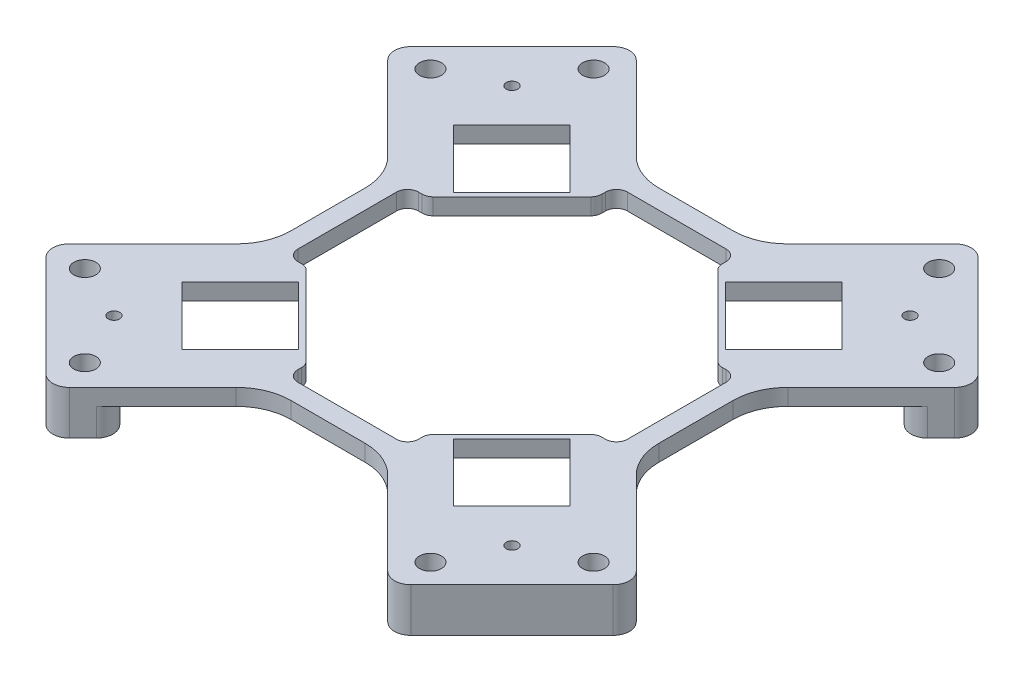
SolidWorks part; units mm, degrees
ref_plane "Front Plane" through (0, 0, 0) normal (0, 0, 1) x (1, 0, 0)
ref_plane "Top Plane" through (0, 0, 0) normal (0, 1, 0) x (1, 0, 0)
ref_plane "Right Plane" through (0, 0, 0) normal (1, 0, 0) x (0, 0, -1)
sketch "Sketch1" plane through (0, 0, 0) normal (0, 1, 0) x (1, 0, 0)
  line L0 (0, 0) -> (38.8909, 38.8909) construction
  line L1 (0, 0) -> (0, 62.2782) construction
  line L2 (0, 0) -> (67.5007, 0) construction
  line L3 (31.4663, 46.3155) -> (46.3155, 31.4663) construction
  circle A0 centre (31.4663, 46.3155) radius 2
  circle A1 centre (46.3155, 31.4663) radius 2
  circle A2 centre (46.3155, -31.4663) radius 2
  circle A3 centre (31.4663, -46.3155) radius 2
  circle A4 centre (-31.4663, -46.3155) radius 2
  circle A5 centre (-46.3155, -31.4663) radius 2
  circle A6 centre (-46.3155, 31.4663) radius 2
  circle A7 centre (-31.4663, 46.3155) radius 2
  dimension "D2" = 4
  dimension "D3" = 21
  dimension "D4" = 110
  dimension "D1" = 45
sketch "Sketch2" plane through (0, 0, 0) normal (0, 1, 0) x (1, 0, 0)
  line L0 (0, 0) -> (-24.7487, 24.7487) construction
  line L1 (0, 0) -> (0, 43.8991) construction
  line L2 (-30.052, 19.4454) -> (-19.4454, 30.052) construction
  line L3 (-35.3553, 24.7487) -> (-24.7487, 35.3553)
  line L4 (-24.7487, 35.3553) -> (-14.1421, 24.7487)
  line L5 (-14.1421, 24.7487) -> (-24.7487, 14.1421)
  line L6 (-24.7487, 14.1421) -> (-35.3553, 24.7487)
  line L7 (14.1421, 24.7487) -> (24.7487, 14.1421)
  line L8 (24.7487, 14.1421) -> (35.3553, 24.7487)
  line L9 (35.3553, 24.7487) -> (24.7487, 35.3553)
  line L10 (24.7487, 35.3553) -> (14.1421, 24.7487)
  line L11 (0, 0) -> (-30.052, 0) construction
  line L12 (-14.1421, -24.7487) -> (-24.7487, -14.1421)
  line L13 (-24.7487, -14.1421) -> (-35.3553, -24.7487)
  line L14 (-35.3553, -24.7487) -> (-24.7487, -35.3553)
  line L15 (-24.7487, -35.3553) -> (-14.1421, -24.7487)
  line L16 (14.1421, -24.7487) -> (24.7487, -14.1421)
  line L17 (24.7487, -35.3553) -> (14.1421, -24.7487)
  line L18 (35.3553, -24.7487) -> (24.7487, -35.3553)
  line L19 (24.7487, -14.1421) -> (35.3553, -24.7487)
  dimension "D1" = 45
  dimension "D2" = 15
  dimension "D3" = 15
  dimension "D4" = 35
sketch "Sketch3" plane through (0, 0, 0) normal (0, 1, 0) x (1, 0, 0)
  line L0 (-53.7401, 31.1127) -> (-31.1127, 53.7401)
  line L1 (-31.1127, 53.7401) -> (31.1127, 53.7401)
  line L2 (31.1127, 53.7401) -> (53.7401, 31.1127)
  line L3 (53.7401, 31.1127) -> (53.7401, -31.1127)
  line L4 (53.7401, -31.1127) -> (31.1127, -53.7401)
  line L5 (31.1127, -53.7401) -> (-31.1127, -53.7401)
  line L6 (-31.1127, -53.7401) -> (-53.7401, -31.1127)
  line L7 (-53.7401, -31.1127) -> (-53.7401, 31.1127)
  line L8 (0, 0) -> (60.9174, 0) construction
  line L9 (0, 0) -> (0, 56.6355) construction
  dimension "D1" = 32
  dimension "D3" = 120
extrude "Boss-Extrude1" add sketch "Sketch3" along normal blind 3
sketch "Sketch4" plane through (0, 0, 0) normal (0, -1, 0) x (-1, 0, 0)
  line L0 (53.7401, -31.1127) -> (31.1127, -53.7401)
  line L1 (31.1127, -53.7401) -> (24.3952, -47.0226)
  line L3 (24.3952, -47.0226) -> (47.0226, -24.3952)
  line L5 (47.0226, -24.3952) -> (53.7401, -31.1127)
  line L6 (0, 0) -> (0, 69.2529) construction
  line L7 (0, 0) -> (88.6109, 0) construction
  line L8 (31.1127, 53.7401) -> (24.3952, 47.0226)
  line L9 (53.7401, 31.1127) -> (31.1127, 53.7401)
  line L10 (47.0226, 24.3952) -> (53.7401, 31.1127)
  line L11 (24.3952, 47.0226) -> (47.0226, 24.3952)
  line L12 (-31.1127, 53.7401) -> (-24.3952, 47.0226)
  line L13 (-53.7401, 31.1127) -> (-31.1127, 53.7401)
  line L14 (-47.0226, 24.3952) -> (-53.7401, 31.1127)
  line L15 (-24.3952, 47.0226) -> (-47.0226, 24.3952)
  line L16 (-47.0226, -24.3952) -> (-53.7401, -31.1127)
  line L17 (-53.7401, -31.1127) -> (-31.1127, -53.7401)
  line L18 (-31.1127, -53.7401) -> (-24.3952, -47.0226)
  line L19 (-24.3952, -47.0226) -> (-47.0226, -24.3952)
  dimension "D1" = 9.5
extrude "Boss-Extrude2" add sketch "Sketch4" along normal blind 5
extrude "Cut-Extrude1" cut sketch "Sketch2" along normal blind 3
extrude "Cut-Extrude2" cut sketch "Sketch1" along normal through all and the other way through all
sketch "Sketch5" plane through (0, 0, 0) normal (0, 1, 0) x (1, 0, 0)
  line L0 (-53.7401, -31.1127) -> (-33.5, -10.8726)
  line L1 (-33.5, -10.8726) -> (-33.5, 10.8726)
  line L2 (-33.5, 10.8726) -> (-53.7401, 31.1127)
  line L3 (-47.0226, 24.3952) -> (-53.7401, 31.1127) construction
  line L4 (-53.7401, 31.1127) -> (-53.7401, -31.1127) construction
  line L5 (-53.7401, 31.1127) -> (-53.7401, -31.1127)
  line L6 (53.7401, -31.1127) -> (33.5, -10.8726)
  line L7 (33.5, -10.8726) -> (33.5, 10.8726)
  line L8 (33.5, 10.8726) -> (53.7401, 31.1127)
  line L9 (53.7401, 31.1127) -> (53.7401, -31.1127)
  line L10 (0, 0) -> (0, 62.7351) construction
  line L11 (-53.7401, 0) -> (53.7401, 0) construction
  line L13 (-31.1127, -53.7401) -> (31.1127, -53.7401)
  line L14 (-31.1127, -53.7401) -> (31.1127, -53.7401) construction
  line L15 (31.1127, -53.7401) -> (10.8726, -33.5)
  line L16 (10.8726, -33.5) -> (-10.8726, -33.5)
  line L17 (-10.8726, -33.5) -> (-31.1127, -53.7401)
  line L18 (-31.1127, 53.7401) -> (31.1127, 53.7401)
  line L19 (31.1127, 53.7401) -> (10.8726, 33.5)
  line L20 (10.8726, 33.5) -> (-10.8726, 33.5)
  line L21 (-10.8726, 33.5) -> (-31.1127, 53.7401)
  dimension "D1" = 67
  dimension "D2" = 45
  dimension "D3" = 67
  dimension "D4" = 45
extrude "Cut-Extrude4" cut sketch "Sketch5" along normal blind 10
fillet "Fillet1" radius 3 16 edges at (-47.0226, -2.5, 24.3952) (-53.7401, -1, 31.1127) (-31.1127, -1, 53.7401) (-24.3952, -2.5, 47.0226) (24.3952, -2.5, 47.0226) (31.1127, -1, 53.7401) (47.0226, -2.5, 24.3952) (53.7401, -1, 31.1127) (47.0226, -2.5, -24.3952) (53.7401, -1, -31.1127) (31.1127, -1, -53.7401) (24.3952, -2.5, -47.0226) (-47.0226, -2.5, -24.3952) (-53.7401, -1, -31.1127) (-24.3952, -2.5, -47.0226) (-31.1127, -1, -53.7401)
fillet "Fillet2" radius 10 8 edges at (33.5, 1.5, 10.8726) (33.5, 1.5, -10.8726) (10.8726, 1.5, -33.5) (-10.8726, 1.5, -33.5) (-33.5, 1.5, -10.8726) (-33.5, 1.5, 10.8726) (-10.8726, 1.5, 33.5) (10.8726, 1.5, 33.5)
sketch "Sketch8" plane through (0, 0, 0) normal (0, -1, 0) x (1, 0, 0)
  line L0 (0, 0) -> (-17.0913, 17.0913) construction
  line L1 (0, 0) -> (17.0913, 17.0913) construction
  line L2 (0, 0) -> (0, 30.4732) construction
  line L3 (-26.5, 10.9767) -> (-10.9767, 26.5)
  line L4 (-10.9767, 26.5) -> (10.9767, 26.5)
  line L5 (10.9767, 26.5) -> (26.5, 10.9767)
  line L6 (26.5, 10.9767) -> (26.5, -10.9767)
  line L7 (26.5, -10.9767) -> (10.9767, -26.5)
  line L8 (10.9767, -26.5) -> (-10.9767, -26.5)
  line L9 (-10.9767, -26.5) -> (-26.5, -10.9767)
  line L10 (-26.5, -10.9767) -> (-26.5, 10.9767)
  line L11 (0, 26.5) -> (0, -26.5) construction
  line L12 (-26.5, 0) -> (26.5, 0) construction
  line L13 (24.7487, 14.1421) -> (14.1421, 24.7487) construction
  dimension "D1" = 45
  dimension "D2" = 1
extrude "Cut-Extrude5" cut sketch "Sketch8" against normal blind 10
sketch "Sketch9" plane through (0, 0, 0) normal (0, -1, 0) x (1, 0, 0)
  line L0 (0, 0) -> (0, 53.3985) construction
  line L1 (-30, -10.9767) -> (-25, -10.9767)
  line L2 (-30, -10.9767) -> (-30, 10.9767)
  line L3 (-30, 10.9767) -> (-25, 10.9767)
  line L4 (-25, -10.9767) -> (-25, 10.9767)
  line L5 (-10.9767, 25) -> (10.9767, 25)
  line L6 (-10.9767, 25) -> (-10.9767, 30)
  line L7 (-10.9767, 30) -> (10.9767, 30)
  line L8 (10.9767, 25) -> (10.9767, 30)
  line L9 (30, -10.9767) -> (25, -10.9767)
  line L10 (30, -10.9767) -> (30, 10.9767)
  line L11 (30, 10.9767) -> (25, 10.9767)
  line L12 (25, -10.9767) -> (25, 10.9767)
  line L13 (-10.9767, -25) -> (10.9767, -25)
  line L14 (-10.9767, -25) -> (-10.9767, -30)
  line L15 (-10.9767, -30) -> (10.9767, -30)
  line L16 (10.9767, -25) -> (10.9767, -30)
  line L17 (0, 0) -> (-45.8524, 0) construction
  dimension "D1" = 50
  dimension "D2" = 50
  dimension "D3" = 60
  dimension "D4" = 60
extrude "Cut-Extrude6" cut sketch "Sketch9" against normal blind 10
fillet "Fillet3" radius 2 16 edges at (-10.9767, 1.5, 26.5) (-10.9767, 1.5, 30) (10.9767, 1.5, 30) (10.9767, 1.5, 26.5) (26.5, 1.5, 10.9767) (30, 1.5, 10.9767) (30, 1.5, -10.9767) (26.5, 1.5, -10.9767) (10.9767, 1.5, -26.5) (10.9767, 1.5, -30) (-10.9767, 1.5, -30) (-10.9767, 1.5, -26.5) (-26.5, 1.5, -10.9767) (-26.5, 1.5, 10.9767) (-30, 1.5, 10.9767) (-30, 1.5, -10.9767)
sketch "Sketch10" plane through (0, 0, 0) normal (0, 1, 0) x (1, 0, 0)
  line L0 (36.2392, 36.2392) -> (-36.2392, -36.2392) construction
  line L1 (-36.2392, 36.2392) -> (36.2392, -36.2392) construction
  line L2 (0, 0) -> (-21.423, 0) construction
  circle A0 centre (36.2392, 36.2392) radius 1.05
  circle A1 centre (-36.2392, -36.2392) radius 1.05
  circle A2 centre (-36.2392, 36.2392) radius 1.05
  circle A3 centre (36.2392, -36.2392) radius 1.05
  dimension "D1" = 2.1
  dimension "D2" = 102.5
  dimension "D3" = 102.5
  dimension "D4" = 45
extrude "Cut-Extrude7" cut sketch "Sketch10" against normal blind 10 and the other way blind 10
sketch "Sketch11" plane through (0, 0, 0) normal (0, -1, 0) x (1, 0, 0)
  circle A0 centre (36.2392, -36.2392) radius 4
  circle A1 centre (-36.2392, 36.2392) radius 4
  circle A2 centre (-36.2392, -36.2392) radius 4
  circle A3 centre (36.2392, 36.2392) radius 4
  circle A4 centre (-36.2392, 36.2392) radius 1.05
  arc A5 (-36.2285, 35.1893) -> (-35.1893, 36.2285) centre (-36.2392, 36.2392) ccw construction
  circle A6 centre (36.2392, 36.2392) radius 1.05
  arc A7 (35.1893, 36.2285) -> (36.2285, 35.1893) centre (36.2392, 36.2392) ccw construction
  circle A8 centre (36.2392, -36.2392) radius 1.05
  arc A9 (36.2285, -35.1893) -> (35.1893, -36.2285) centre (36.2392, -36.2392) ccw construction
  circle A10 centre (-36.2392, -36.2392) radius 1.05
  arc A11 (-35.1893, -36.2285) -> (-36.2285, -35.1893) centre (-36.2392, -36.2392) ccw construction
  dimension "D1" = 8
extrude "Boss-Extrude3" add sketch "Sketch11" along normal blind 2
sketch "Sketch13" plane through (0, -2, 0) normal (0, -1, 0) x (1, 0, 0)
  circle A0 centre (-36.2392, 36.2392) radius 4
  arc A1 (-38.4872, 32.9306) -> (-32.9306, 38.4872) centre (-36.2392, 36.2392) ccw construction
  circle A2 centre (36.2392, 36.2392) radius 4
  circle A3 centre (36.2392, -36.2392) radius 4
  circle A4 centre (-36.2392, -36.2392) radius 4
  arc A5 (-32.9306, -38.4872) -> (-38.4872, -32.9306) centre (-36.2392, -36.2392) ccw construction
  arc A6 (38.4872, -32.9306) -> (32.9306, -38.4872) centre (36.2392, -36.2392) ccw construction
  arc A7 (32.9306, 38.4872) -> (38.4872, 32.9306) centre (36.2392, 36.2392) ccw construction
extrude "Cut-Extrude9" cut sketch "Sketch13" along normal blind 10
